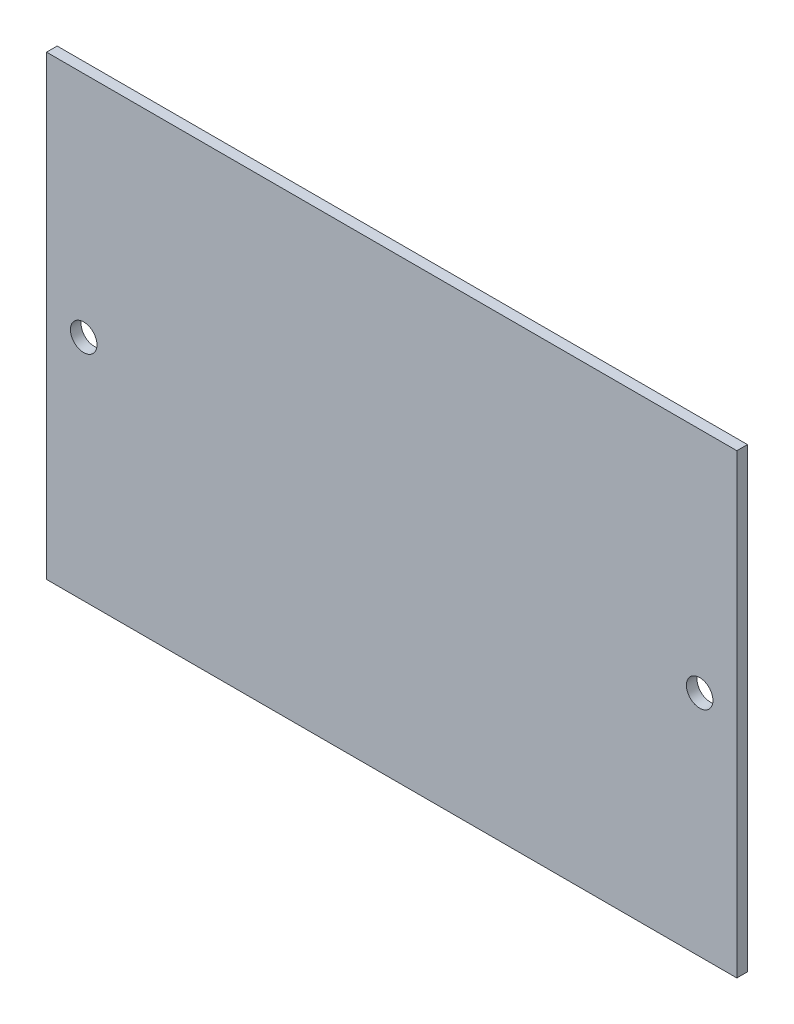
SolidWorks part; units mm, degrees
ref_plane "Front Plane" through (0, 0, 0) normal (0, 0, 1) x (1, 0, 0)
ref_plane "Top Plane" through (0, 0, 0) normal (0, 1, 0) x (1, 0, 0)
ref_plane "Right Plane" through (0, 0, 0) normal (1, 0, 0) x (0, 0, -1)
sketch "Sketch1" plane through (0, 0, 0) normal (0, 0, 1) x (1, 0, 0)
  line L1 (-65, 43) -> (65, 43)
  line L2 (-65, 43) -> (-65, -43)
  line L3 (-65, -43) -> (65, -43)
  line L4 (65, 43) -> (65, -43)
  line L5 (-65, 43) -> (65, -43) construction
  line L6 (-65, -43) -> (65, 43) construction
  circle A2 centre (-58, 0) radius 2.5
  circle A3 centre (58, 0) radius 2.5
  point P0 (0, 0)
  dimension "D3" = 7
  dimension "D4" = 7
  dimension "D1" = 130
  dimension "D2" = 86
  dimension "D5" = 43
  dimension "D6" = 43
extrude "Boss-Extrude1" add sketch "Sketch1" along normal blind 2
